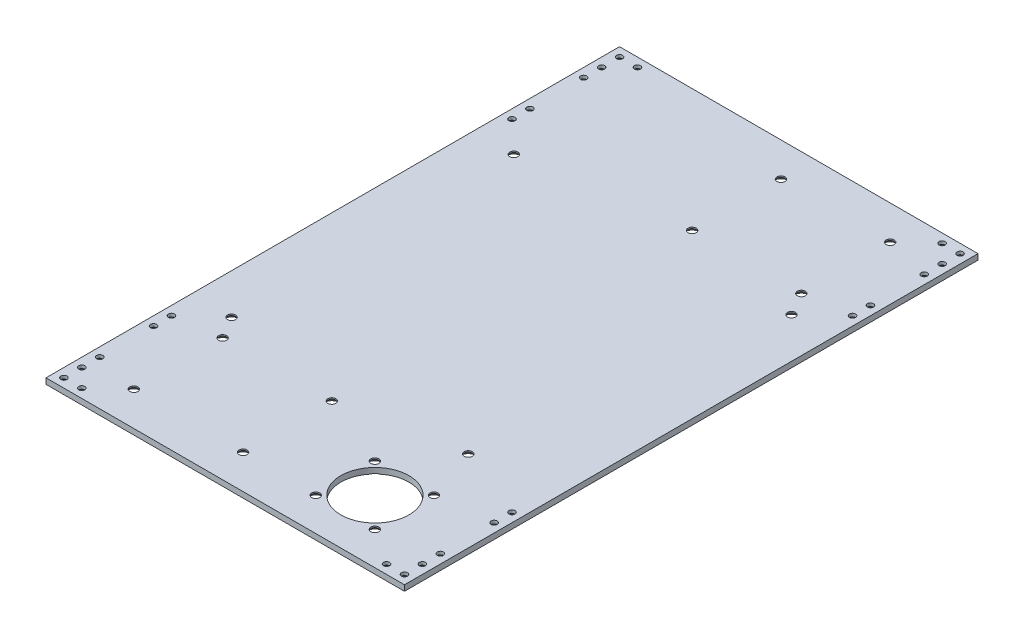
SolidWorks part; units mm, degrees
material "Garolite (G-10/FR4)"
ref_plane "Front Plane" through (0, 0, 0) normal (0, 0, 1) x (1, 0, 0)
ref_plane "Top Plane" through (0, 0, 0) normal (0, 1, 0) x (1, 0, 0)
ref_plane "Right Plane" through (0, 0, 0) normal (1, 0, 0) x (0, 0, -1)
sketch "Sketch1" plane through (0, 0, 0) normal (0, 1, 0) x (1, 0, 0)
  line L0 (0, -160) -> (0, 160) construction
  line L1 (-100, 160) -> (100, 160)
  line L2 (-100, 160) -> (-100, -160)
  line L3 (-100, -160) -> (100, -160)
  line L4 (100, 160) -> (100, -160)
  line L5 (100, 0) -> (-100, 0) construction
  dimension "D1" = 320
  dimension "D2" = 200
extrude "Boss-Extrude1" add sketch "Sketch1" along normal blind 3.175
hole_wizard "CSK for M3 Flat Head Machine Screw1" positions "Sketch3" profile "Sketch2" countersink size "M3" standard "Ansi Metric" end condition through all
sketch "Sketch3" plane through (0, 0, 0) normal (0, -1, 0) x (1, 0, 0)
  line L0 (-100, 155) -> (-85, 155) construction
  line L1 (-100, -160) -> (-100, 160) construction
  line L3 (-95, 95) -> (-95, 160) construction
  line L4 (-100, 160) -> (100, 160) construction
  line L6 (-100, -160) -> (-100, 160) construction
  point P0 (-95, 155)
  point P1 (-85, 155)
  point P3 (-95, 145)
  point P5 (-95, 135)
  point P40 (-95, 105)
  point P42 (-95, 95)
  dimension "D1" = 10
  dimension "D2" = 10
  dimension "D3" = 10
  dimension "D4" = 5
  dimension "D5" = 5
  dimension "D6" = 10
  dimension "D7" = 30
sketch "Sketch2" plane through (-95, 0, 155) normal (1, 0, 0) x (0, 0, -1)
  line L0 (0, 0) -> (0, 3.175)
  line L1 (0, 3.175) -> (1.7, 3.175)
  line L2 (1.7, 3.175) -> (1.7, 1.45)
  line L3 (1.7, 1.45) -> (3.15, 0)
  line L5 (3.15, 0) -> (0, 0)
  line L6 (-1.7, 1.45) -> (-3.15, 0) construction
  line L11 (0, -6.35) -> (0, 107.95) construction
  dimension "Thru Hole Dia." = 3.4
  dimension "Thru Hole Depth" = 3.175
  dimension "Near C'Sink Dia." = 6.3
  dimension "Near C'Sink Angle" = 90
mirror "Mirror1" about plane through (0, 0, 0) normal (1, 0, 0) of "CSK for M3 Flat Head Machine Screw1"
mirror "Mirror2" about plane through (0, 0, 0) normal (0, 0, 1) of "Mirror1", "CSK for M3 Flat Head Machine Screw1"
hole_wizard "CSK for M4 Flat Head Machine Screw1" positions "Sketch7" profile "Sketch6" countersink size "M4" standard "Ansi Metric" end condition through all
sketch "Sketch7" plane through (0, 0, 0) normal (0, -1, 0) x (1, 0, 0)
  line L1 (65, 108.5) -> (32, 108.5)
  line L2 (65, 108.5) -> (65, 141.5)
  line L3 (65, 141.5) -> (32, 141.5)
  line L4 (32, 108.5) -> (32, 141.5)
  line L6 (-9.04, 91.47) -> (-70, 91.47)
  line L7 (-9.04, 91.47) -> (-9.04, 141)
  line L8 (-9.04, 141) -> (-70, 141)
  line L9 (-70, 91.47) -> (-70, 141)
  line L11 (9.04, -141) -> (70, -141)
  line L12 (9.04, -141) -> (9.04, -91.47)
  line L13 (9.04, -91.47) -> (70, -91.47)
  line L14 (70, -141) -> (70, -91.47)
  line L15 (-100, 160) -> (100, 160) construction
  line L16 (100, 160) -> (100, -160) construction
  line L17 (-100, -160) -> (-100, 160) construction
  line L18 (100, -160) -> (-100, -160) construction
  line L20 (-77.47, -78.48) -> (77.47, -78.48)
  line L21 (-77.47, -78.48) -> (-77.47, 79)
  line L22 (-77.47, 79) -> (77.47, 79)
  line L23 (77.47, -78.48) -> (77.47, 79)
  line L25 (-77.47, 0.26) -> (-100, 0.26) construction
  line L27 (77.47, 0.26) -> (100, 0.26) construction
  line L29 (100, 160) -> (100, -160) construction
  line L30 (-100, -160) -> (-100, 160) construction
  line L31 (-100, 160) -> (100, 160) construction
  point P0 (-9.04, 91.47)
  point P1 (32, 141.5)
  point P3 (32, 108.5)
  point P5 (65, 108.5)
  point P7 (-70, 141)
  point P9 (-70, 91.47)
  point P11 (-9.04, 141)
  point P13 (65, 141.5)
  point P15 (70, -141)
  point P17 (9.04, -141)
  point P19 (9.04, -91.47)
  point P21 (70, -91.47)
  point P375 (54.61, 79)
  point P377 (77.47, -78.48)
  point P379 (-77.47, -78.48)
  point P381 (-77.47, 79)
  dimension "D1" = 33
  dimension "D2" = 18.5
  dimension "D3" = 35
  dimension "D4" = 60.96
  dimension "D5" = 49.53
  dimension "D6" = 19
  dimension "D7" = 30
  dimension "D8" = 19
  dimension "D9" = 30
  dimension "D10" = 154.94
  dimension "D11" = 22.86
  dimension "D12" = 157.48
  dimension "D13" = 81
sketch "Sketch6" plane through (-9.04, 0, 91.47) normal (1, 0, 0) x (0, 0, -1)
  line L0 (0, 0) -> (0, 3.175)
  line L1 (0, 3.175) -> (2.25, 3.175)
  line L2 (2.25, 3.175) -> (2.25, 2.45)
  line L3 (2.25, 2.45) -> (4.7, 0)
  line L5 (4.7, 0) -> (0, 0)
  line L6 (-2.25, 2.45) -> (-4.7, 0) construction
  line L11 (0, -6.35) -> (0, 107.95) construction
  dimension "Thru Hole Dia." = 4.5
  dimension "Thru Hole Depth" = 3.175
  dimension "Near C'Sink Dia." = 9.4
  dimension "Near C'Sink Angle" = 90
sketch "Sketch8" plane through (0, 3.175, 0) normal (0, 1, 0) x (1, 0, 0)
  line L0 (65, -141.5) -> (32, -108.5) construction
  line L1 (32, -141.5) -> (65, -108.5) construction
  circle A0 centre (48.5, -125) radius 19
  dimension "D1" = 38
extrude "Cut-Extrude1" cut sketch "Sketch8" against normal through all
